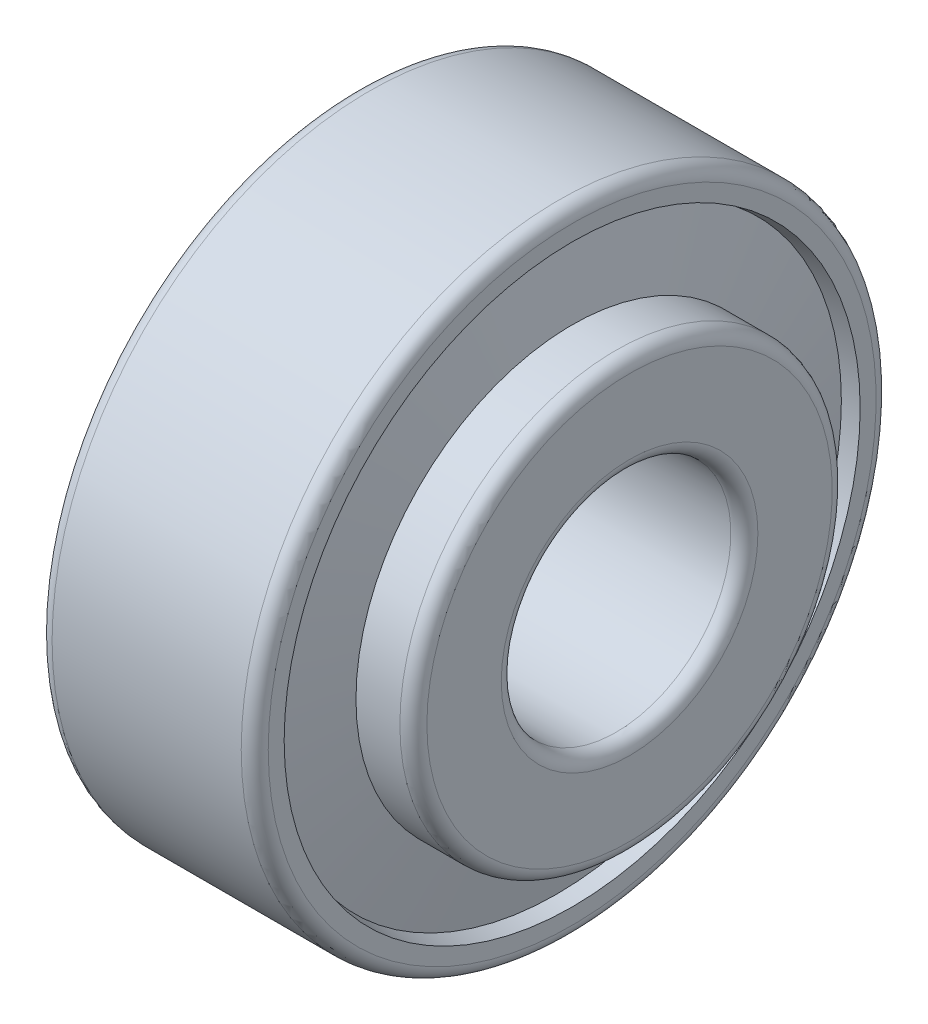
SolidWorks part; units mm, degrees
material "AISI Тип A2 Инструментальная сталь"
ref_plane "Спереди" through (0, 0, 0) normal (0, 0, 1) x (1, 0, 0)
ref_plane "Сверху" through (0, 0, 0) normal (0, 1, 0) x (1, 0, 0)
ref_plane "Справа" through (0, 0, 0) normal (1, 0, 0) x (0, 0, -1)
sketch "Эскиз1" plane through (0, 0, 0) normal (0, 0, 1) x (1, 0, 0)
  line L20 (-882.5277, 0) -> (43243.8573, 0) construction
  line L33 (2.3374, 18.5236) -> (0, 18.045)
  line L34 (0, 18.045) -> (0, 22.5)
  line L35 (1, 23.5) -> (15, 23.5)
  line L36 (16, 22.5) -> (16, 21.321)
  line L37 (16, 21.321) -> (14.845, 21.0845)
  line L38 (2.3374, 18.5236) -> (14.845, 21.0845) construction
  line L39 (3.4247, 12.8006) -> (1.25, 12.8006)
  line L40 (1.25, 12.8006) -> (1.25, 9.5)
  line L41 (2.25, 8.5) -> (19.25, 8.5)
  line L42 (20.25, 9.5) -> (20.25, 15.0055)
  line L43 (19.25, 16.0055) -> (16, 16.0055)
  line L44 (16, 16.0055) -> (16, 15.0055)
  line L45 (3.4247, 12.8006) -> (16, 15.0055) construction
  line L46 (16, 15.0055) -> (14.845, 21.0845)
  line L47 (3.4247, 12.8006) -> (2.3374, 18.5236)
  line L48 (2.8811, 15.6621) -> (15.4225, 18.045) construction
  line L49 (0, 18.045) -> (15.4225, 18.045) construction
  line L50 (2.3374, 18.5236) -> (2.3374, 12.8006) construction
  arc A0 (0, 22.5) -> (1, 23.5) centre (1, 22.5) cw
  arc A1 (15, 23.5) -> (16, 22.5) centre (15, 22.5) cw
  arc A2 (1.25, 9.5) -> (2.25, 8.5) centre (2.25, 9.5) ccw
  arc A3 (20.25, 9.5) -> (19.25, 8.5) centre (19.25, 9.5) cw
  arc A4 (19.25, 16.0055) -> (20.25, 15.0055) centre (19.25, 15.0055) cw
  point P12 (15.4225, 18.045)
  dimension "гост r1" = 1
  dimension "гост r2" = 1
  dimension "гост DD" = 47
  dimension "гост B" = 19
  dimension "гост C" = 16
  dimension "гост T" = 20.25
  dimension "гост E" = 36.09
  dimension "гост d" = 17
  dimension "гост alfa" = 10.758
revolve "Повернуть1" add sketch "Эскиз1" angle 360 about L20
